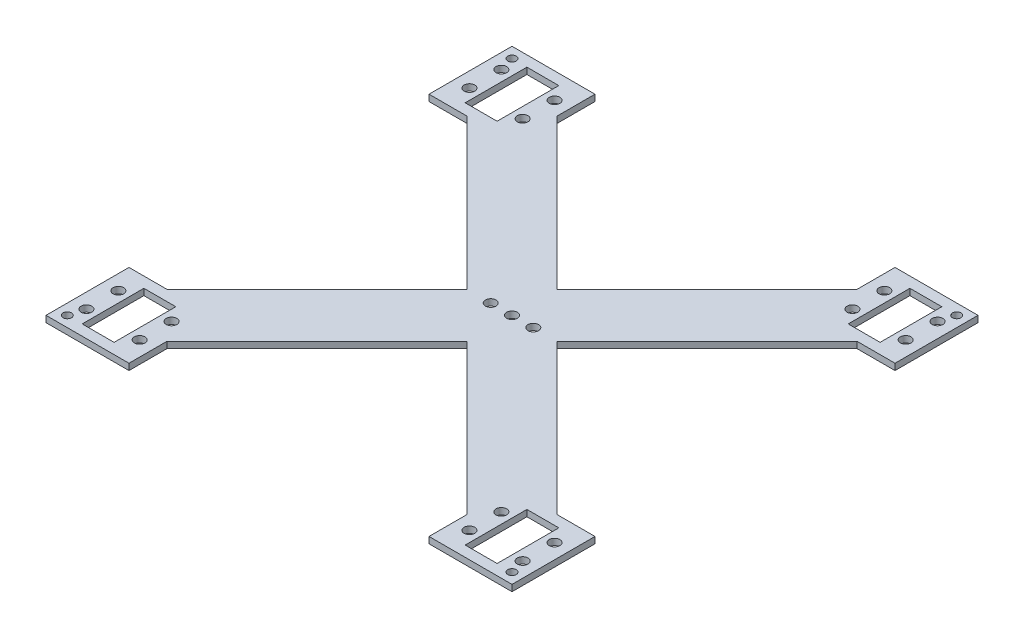
SolidWorks part; units mm, degrees
ref_plane "Front Plane" through (0, 0, 0) normal (0, 0, 1) x (1, 0, 0)
ref_plane "Top Plane" through (0, 0, 0) normal (0, 1, 0) x (1, 0, 0)
ref_plane "Right Plane" through (0, 0, 0) normal (1, 0, 0) x (0, 0, -1)
sketch "Sketch1" plane through (0, 0, 0) normal (0, 1, 0) x (1, 0, 0)
  line L0 (-70.5, -91.7132) -> (0, -21.2132)
  line L1 (-109.5, -109.5) -> (-70.5, -109.5)
  line L2 (-109.5, -109.5) -> (-109.5, -70.5)
  line L3 (-109.5, -70.5) -> (-91.7132, -70.5)
  line L4 (-70.5, -109.5) -> (-70.5, -91.7132)
  line L5 (0, -21.2132) -> (0, 0) construction
  line L6 (0, 0) -> (-21.2132, 0) construction
  line L7 (-21.2132, 0) -> (-91.7132, -70.5)
  line L8 (-90, -75.5) -> (-90, -104.5) construction
  line L9 (-97.5, -104.5) -> (-82.5, -104.5)
  line L10 (-97.5, -104.5) -> (-97.5, -75.5)
  line L11 (-97.5, -75.5) -> (-82.5, -75.5)
  line L12 (-82.5, -104.5) -> (-82.5, -75.5)
  line L13 (-97.5, -90) -> (-109.5, -90) construction
  line L14 (-97.5, -90) -> (-82.5, -90) construction
  line L15 (-70.5, -91.7132) -> (-82.5, -91.7132) construction
  line L16 (-90, -104.5) -> (-90, -109.5) construction
  line L17 (-90, -75.5) -> (-90, -70.5) construction
  line L18 (21.2132, 0) -> (91.7132, -70.5)
  line L19 (70.5, -91.7132) -> (0, -21.2132)
  line L20 (90, -75.5) -> (90, -70.5) construction
  line L21 (90, -104.5) -> (90, -109.5) construction
  line L22 (70.5, -91.7132) -> (82.5, -91.7132) construction
  line L23 (97.5, -90) -> (82.5, -90) construction
  line L24 (97.5, -90) -> (109.5, -90) construction
  line L25 (90, -75.5) -> (90, -104.5) construction
  line L26 (82.5, -104.5) -> (82.5, -75.5)
  line L27 (97.5, -75.5) -> (82.5, -75.5)
  line L28 (97.5, -104.5) -> (97.5, -75.5)
  line L29 (97.5, -104.5) -> (82.5, -104.5)
  line L30 (70.5, -109.5) -> (70.5, -91.7132)
  line L31 (109.5, -70.5) -> (91.7132, -70.5)
  line L32 (109.5, -109.5) -> (109.5, -70.5)
  line L33 (109.5, -109.5) -> (70.5, -109.5)
  line L34 (90, 75.5) -> (90, 104.5) construction
  line L35 (97.5, 90) -> (109.5, 90) construction
  line L36 (97.5, 90) -> (82.5, 90) construction
  line L37 (70.5, 91.7132) -> (82.5, 91.7132) construction
  line L38 (90, 104.5) -> (90, 109.5) construction
  line L39 (90, 75.5) -> (90, 70.5) construction
  line L40 (-90, 75.5) -> (-90, 70.5) construction
  line L41 (-90, 104.5) -> (-90, 109.5) construction
  line L42 (-70.5, 91.7132) -> (-82.5, 91.7132) construction
  line L43 (-97.5, 90) -> (-82.5, 90) construction
  line L44 (-97.5, 90) -> (-109.5, 90) construction
  line L45 (-90, 75.5) -> (-90, 104.5) construction
  line L46 (109.5, 109.5) -> (70.5, 109.5)
  line L47 (109.5, 109.5) -> (109.5, 70.5)
  line L48 (109.5, 70.5) -> (91.7132, 70.5)
  line L49 (70.5, 109.5) -> (70.5, 91.7132)
  line L50 (97.5, 104.5) -> (82.5, 104.5)
  line L51 (97.5, 104.5) -> (97.5, 75.5)
  line L52 (97.5, 75.5) -> (82.5, 75.5)
  line L53 (82.5, 104.5) -> (82.5, 75.5)
  line L54 (70.5, 91.7132) -> (0, 21.2132)
  line L55 (21.2132, 0) -> (91.7132, 70.5)
  line L56 (-82.5, 104.5) -> (-82.5, 75.5)
  line L57 (-97.5, 75.5) -> (-82.5, 75.5)
  line L58 (-97.5, 104.5) -> (-97.5, 75.5)
  line L59 (-97.5, 104.5) -> (-82.5, 104.5)
  line L60 (-21.2132, 0) -> (-91.7132, 70.5)
  line L61 (-70.5, 109.5) -> (-70.5, 91.7132)
  line L62 (-109.5, 70.5) -> (-91.7132, 70.5)
  line L63 (-109.5, 109.5) -> (-109.5, 70.5)
  line L64 (-109.5, 109.5) -> (-70.5, 109.5)
  line L65 (-70.5, 91.7132) -> (0, 21.2132)
  circle A0 centre (-104.5, -104.5) radius 2
  circle A1 centre (-102.5, -82.5) radius 2.5
  circle A2 centre (-77.5, -82.5) radius 2.5
  circle A3 centre (-77.5, -97.5) radius 2.5
  circle A4 centre (-102.5, -97.5) radius 2.5
  circle A5 centre (102.5, -97.5) radius 2.5
  circle A6 centre (77.5, -97.5) radius 2.5
  circle A7 centre (77.5, -82.5) radius 2.5
  circle A8 centre (102.5, -82.5) radius 2.5
  circle A9 centre (104.5, -104.5) radius 2
  circle A10 centre (104.5, 104.5) radius 2
  circle A11 centre (102.5, 82.5) radius 2.5
  circle A12 centre (77.5, 82.5) radius 2.5
  circle A13 centre (77.5, 97.5) radius 2.5
  circle A14 centre (102.5, 97.5) radius 2.5
  circle A15 centre (-102.5, 97.5) radius 2.5
  circle A16 centre (-77.5, 97.5) radius 2.5
  circle A17 centre (-77.5, 82.5) radius 2.5
  circle A18 centre (-102.5, 82.5) radius 2.5
  circle A19 centre (-104.5, 104.5) radius 2
  circle A20 centre (0, 0) radius 2.5
  circle A21 centre (-10, 0) radius 2.5
  circle A22 centre (10, 0) radius 2.5
  point P1 (-90, -104.5)
  point P36 (10.4672, 0)
  dimension "D4" = 4
  dimension "D5" = 104.5
  dimension "D6" = 5
  dimension "D7" = 5
  dimension "D8" = 5
  dimension "D9" = 104.5
  dimension "D14" = 5
  dimension "D15" = 20
  dimension "D1" = 29
  dimension "D2" = 15
  dimension "D3" = 90
  dimension "D10" = 5
  dimension "D11" = 5
  dimension "D12" = 30
  dimension "D13" = 15
extrude "Boss-Extrude1" add sketch "Sketch1" along normal blind 3
